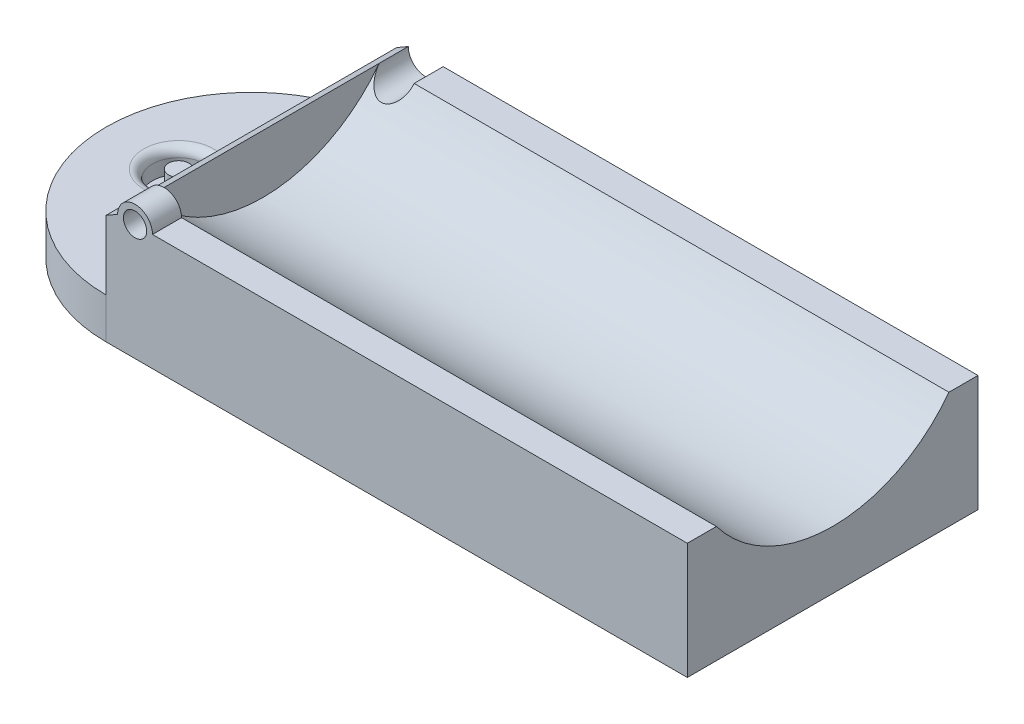
SolidWorks part; units mm, degrees
ref_plane "Front Plane" through (0, 0, 0) normal (0, 0, 1) x (1, 0, 0)
ref_plane "Top Plane" through (0, 0, 0) normal (0, 1, 0) x (1, 0, 0)
ref_plane "Right Plane" through (0, 0, 0) normal (1, 0, 0) x (0, 0, -1)
sketch "Sketch1" plane through (0, 0, 0) normal (0, 1, 0) x (1, 0, 0)
  line L0 (0, 0) -> (100, 0)
  line L1 (100, 0) -> (100, 50)
  line L2 (100, 50) -> (0, 50)
  line L3 (0, 50) -> (0, 0)
  dimension "D1" = 100
  dimension "D2" = 50
extrude "Boss-Extrude1" add sketch "Sketch1" along normal blind 20 contours L0 L1 L2 L3
sketch "Sketch2" plane through (100, 0, 0) normal (1, 0, 0) x (0, 0, -1)
  line L0 (0, 20) -> (0, 0)
  line L1 (0, 0) -> (50, 0)
  line L2 (50, 0) -> (50, 20)
  line L3 (50, 20) -> (45, 20)
  line L4 (0, 20) -> (50, 20) construction
  line L5 (0, 20) -> (5, 20)
  line L6 (5, 20) -> (45, 20)
  arc A0 (5, 20) -> (45, 20) centre (25, 35) ccw
  line M9 (50, 20) -> (0, 20)
  dimension "D2" = 25
  dimension "D1" = 5
  dimension "D3" = 5
  dimension "D4" = 15
sketch "Sketch4" plane through (0, 0, 0) normal (-1, 0, 0) x (0, 0, 1)
  line L2 (0, 20) -> (0, 0) construction
  line L3 (0, 7) -> (0, 0)
  line L6 (-25, 0) -> (-25, 7)
  line L8 (-25, 7) -> (0, 7)
  line L9 (-25, 0) -> (0, 0)
  dimension "D1" = 25
  dimension "D2" = 7
revolve "Revolve1" add sketch "Sketch4" angle 360 about L6
extrude "Cut-Extrude1" cut sketch "Sketch2" against normal blind 100 contours A0 M9
sketch "Sketch5" plane through (0, 7, 0) normal (0, 1, 0) x (1, 0, 0)
  line L0 (0, 45) -> (0, 5) construction
  line L1 (100, 50) -> (0, 50) construction
  circle A0 centre (-12.5, 25) radius 1.75
  circle A1 centre (-12.5, 25) radius 4.5
  dimension "D1" = 3.5
  dimension "D2" = 9
  dimension "D3" = 12.5
  dimension "D4" = 25
extrude "Cut-Extrude2" cut sketch "Sketch5" against normal blind 4
fillet "Fillet2" radius 1.5 1 edges at (-12.5, 7, -20.5)
sketch "Sketch6" plane through (0, 0, 0) normal (0, 0, 1) x (1, 0, 0)
  line L0 (0, 20) -> (100, 20) construction
  line L1 (0, 20) -> (0, 7) construction
  circle A0 centre (5, 20) radius 2
  circle A1 centre (5, 20) radius 3
  dimension "D3" = 4
  dimension "D4" = 6
  dimension "D1" = 0
  dimension "D2" = 5
extrude "Boss-Extrude3" add sketch "Sketch6" against normal blind 5
sketch "Sketch8" plane through (0, 0, 0) normal (0, 0, 1) x (1, 0, 0)
  line L0 (3, 20) -> (7, 20)
  arc A0 (3, 20) -> (7, 20) centre (5, 20) ccw
extrude "Cut-Extrude3" cut sketch "Sketch8" against normal blind 10
sketch "Sketch10" plane through (0, 0, -50) normal (0, 0, -1) x (-1, 0, 0)
  line L0 (-100, 20) -> (0, 20) construction
  line L1 (0, 20) -> (0, 7) construction
  circle A1 centre (-5, 20) radius 3
  dimension "D3" = 6
  dimension "D1" = 5
extrude "Cut-Extrude4" cut sketch "Sketch10" against normal blind 10
sketch "Sketch11" plane through (0, 0, -50) normal (0, 0, -1) x (-1, 0, 0)
  line L0 (-2, 20) -> (0, 18.8453)
  line L1 (0, 20) -> (0, 7) construction
  line L2 (0, 18.8453) -> (0, 20)
  line L3 (0, 20) -> (-2, 20)
  dimension "D1" = 30
extrude "Cut-Extrude5" cut sketch "Sketch11" against normal blind 54
sketch "Sketch12" plane through (0, 0, -50) normal (0, 0, -1) x (-1, 0, 0)
  line L0 (-2, 20) -> (-2, 0)
  line L1 (-2, 20) -> (0, 18.8453) construction
  line L2 (-100, 0) -> (0, 0) construction
  line L3 (-2, 0) -> (0, 0)
  line L4 (0, 0) -> (0, 18.8453)
  line L5 (0, 18.8453) -> (-2, 20)
  arc A0 (-8, 20) -> (-2, 20) centre (-5, 20) ccw construction
extrude "Boss-Extrude4" add sketch "Sketch12" against normal blind 50
